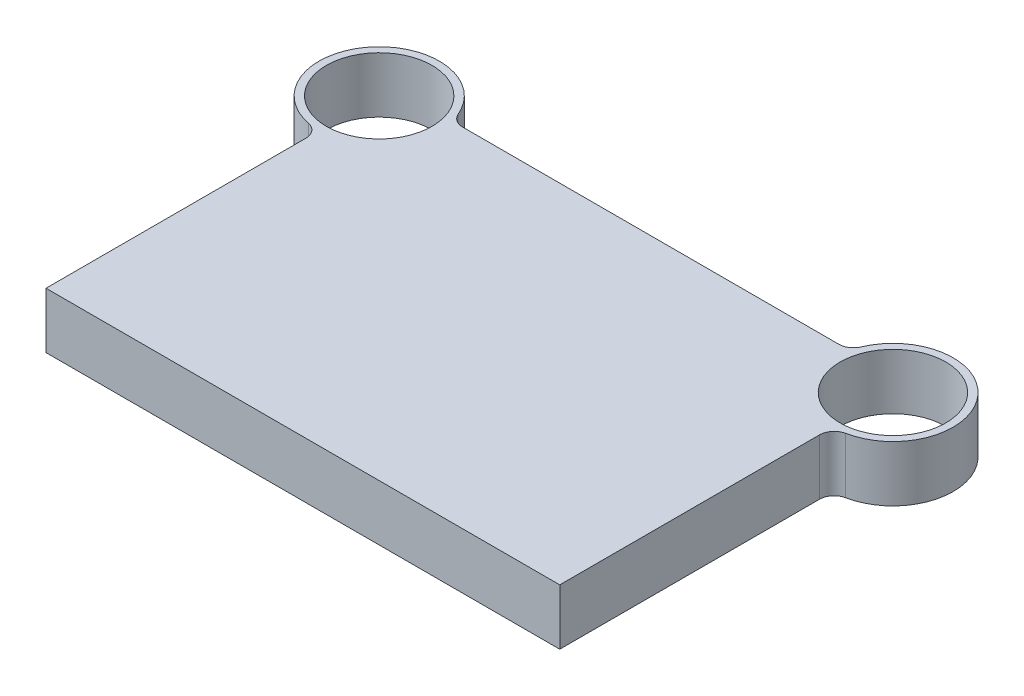
SolidWorks part; units mm, degrees
ref_plane "Front Plane" through (0, 0, 0) normal (0, 0, 1) x (1, 0, 0)
ref_plane "Top Plane" through (0, 0, 0) normal (0, 1, 0) x (1, 0, 0)
ref_plane "Right Plane" through (0, 0, 0) normal (1, 0, 0) x (0, 0, -1)
sketch "Sketch1" plane through (0, 0, 0) normal (0, 1, 0) x (1, 0, 0)
  line L0 (175, 0) -> (-175, 0)
  line L1 (-175, 0) -> (-175, 186)
  line L2 (0, 0) -> (0, 237) construction
  line L3 (135.2382, 237) -> (-135.2382, 237)
  line L4 (175, 0) -> (175, 186)
  arc A0 (-135.2382, 237) -> (-175, 186) centre (-175, 227) ccw
  circle A1 centre (-175, 227) radius 36
  arc A2 (135.2382, 237) -> (175, 186) centre (175, 227) cw
  circle A3 centre (175, 227) radius 36
  point P9 (-158.9154, 238.3731)
  point P10 (-183.5216, 201.7927)
  point P11 (-118.1115, 255.0655)
  point P12 (0, 0)
  dimension "D3" = 82
  dimension "D4" = 72
  dimension "D1" = 227
  dimension "D2" = 237
  dimension "D5" = 350
  dimension "D6" = 350
extrude "Boss-Extrude1" add sketch "Sketch1" along normal blind 38
fillet "Fillet1" radius 10 4 edges at (175, 19, -186) (135.2382, 19, -237) (-135.2382, 19, -237) (-175, 19, -186)
